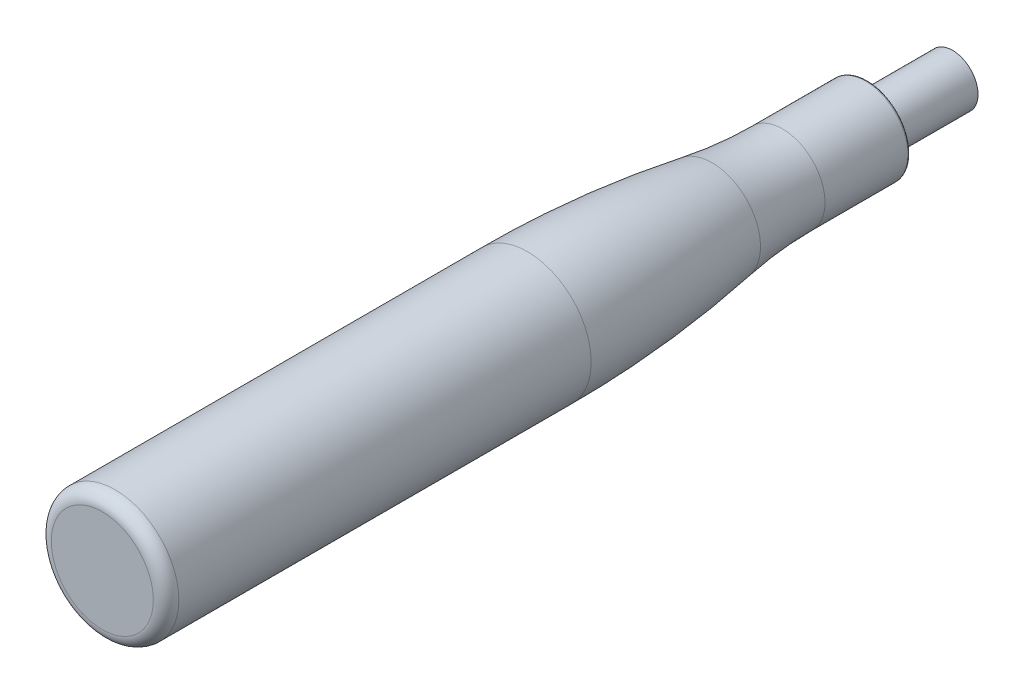
SolidWorks part; units mm, degrees
ref_plane "Front" through (0, 0, 0) normal (0, 0, 1) x (1, 0, 0)
ref_plane "Top" through (0, 0, 0) normal (0, 1, 0) x (1, 0, 0)
ref_plane "Right" through (0, 0, 0) normal (1, 0, 0) x (0, 0, -1)
sketch "Sketch2" plane through (0, 0, 0) normal (1, 0, 0) x (0, 0, -1)
  line L0 (-90, 0) -> (10, 0)
  line L1 (-90, 0) -> (-90, 7.5)
  line L2 (-90, 7.5) -> (-40, 7.5)
  line L3 (0, 124.1457) -> (0, -166.4758) construction
  line L4 (121.4172, 0) -> (-144.9727, 0) construction
  line L5 (10, 0) -> (10, 3)
  line L6 (10, 3) -> (0, 3)
  line L7 (0, 3) -> (0, 5)
  line L8 (0, 5) -> (-10, 5)
  arc A0 (-10, 5) -> (-18.2759, 5.6897) centre (-10, 55) cw
  arc A1 (-18.2759, 5.6897) -> (-40, 7.5) centre (-40, -123.75) ccw
  dimension "D8" = 50
  dimension "D1" = 90
  dimension "D2" = 15
  dimension "D3" = 50
  dimension "D4" = 6
  dimension "D5" = 10
  dimension "D6" = 10
  dimension "D7" = 10
revolve "Revolve1" add sketch "Sketch2" angle 360 about L4
fillet "Fillet1" radius 1.5 1 edges at (-7.5, 0, 90)
fillet "Fillet2" radius 0.25 1 edges at (-5, 0, 0)
